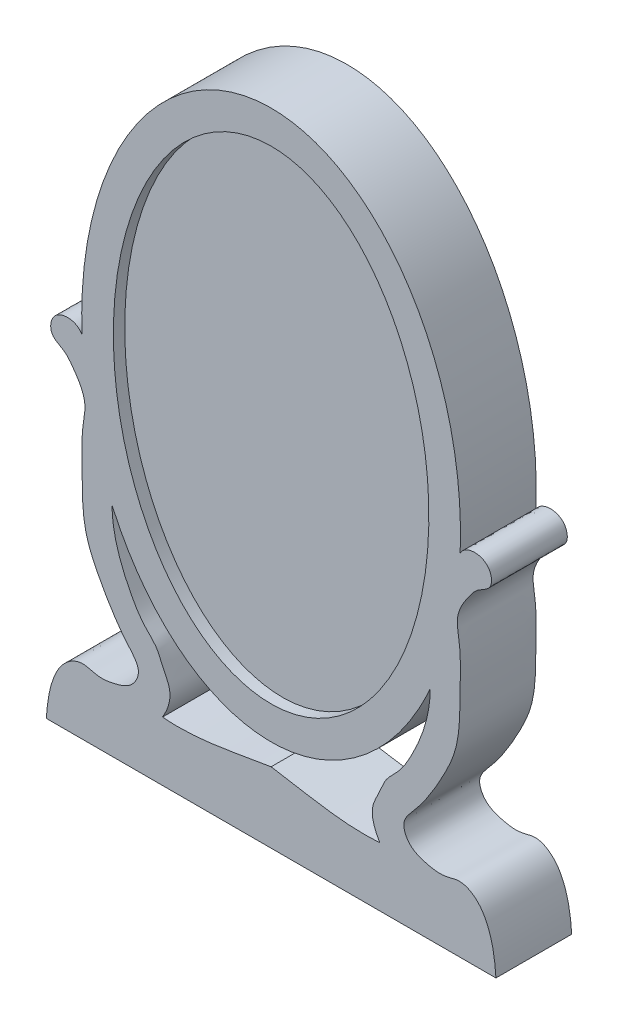
SolidWorks part; units mm, degrees
material "6061 Alloy"
ref_plane "Front Plane" through (0, 0, 0) normal (0, 0, 1) x (1, 0, 0)
ref_plane "Top Plane" through (0, 0, 0) normal (0, 1, 0) x (1, 0, 0)
ref_plane "Right Plane" through (0, 0, 0) normal (1, 0, 0) x (0, 0, -1)
sketch "Sketch1" plane through (0, 0, 0) normal (0, 0, 1) x (1, 0, 0)
  ellipse E0 centre (0, 0) end of major axis (0, 18.4068) minor radius 12.7
  ellipse E1 centre (0, 0) end of major axis (0, 16.1956) minor radius 10.5779
  dimension "D1" = 25.4
extrude "Boss-Extrude1" add sketch "Sketch1" along normal blind 5.08 contours E0 E1
sketch "Sketch3" plane through (0, 0, 0) normal (0, 0, 1) x (1, 0, 0)
  line L0 (-58.3604, 222.4715) -> (456.3062, 222.4715) construction
  line L1 (-15.0737, -24.5751) -> (15.0737, -24.5751)
  line L2 (0, -24.5751) -> (0, -16.9802) construction
  ellipse E0 centre (0, 0) end of major axis (0, 16.1956) minor radius 10.5779 construction
  ellipse E1 centre (0, 0) end of major axis (0, 16.1956) minor radius 10.5779
  ellipse E2 centre (0, 0) end of major axis (0, 18.4068) minor radius 12.7 construction
  ellipse E3 centre (0, 0) end of major axis (0, 18.4068) minor radius 12.7
  spline S0 degree 3 poles (-12.6771, -1.1047) (-13.0147, -0.4447) (-14.6864, -0.3765) (-14.9011, -2.2035) (-13.8469, -2.5536) (-13.1067, -3.5285) (-12.3218, -4.7223) (-12.5933, -6.0613) (-12.723, -7.3548) (-12.6355, -9.5358) (-12.7153, -12.1338) (-11.5521, -14.6416) (-10.5924, -16.2889) (-9.608, -17.5998) (-8.6693, -18.5874) (-9.2548, -19.8824) (-10.4033, -20.2836) (-11.5867, -20.4812) (-12.6745, -20.0175) (-13.9505, -20.6484) (-14.8367, -22.2902) (-15.0182, -23.7173) (-15.0737, -24.5751) knots 0 0 0 0 0.066937 0.100724 0.132255 0.158396 0.217811 0.257919 0.283383 0.341892 0.465467 0.523432 0.602214 0.644588 0.683893 0.717443 0.758397 0.79519 0.829587 0.863768 0.918492 1 1 1 1
  spline S1 degree 3 poles (0, -19.8465) (-2.4132, -20.2161) (-4.8225, -20.8172) (-7.2824, -20.6027) knots 0 0 0 0 1 1 1 1
  spline S2 degree 3 poles (-7.2824, -20.6027) (-6.9834, -20.1098) (-6.5175, -18.9769) (-7.2607, -17.7808) (-7.6401, -16.6788) (-8.6625, -15.8172) (-9.9534, -13.6012) (-10.6596, -11.5758) (-10.6691, -9.9847) knots 0 0 0 0 0.156869 0.26988 0.345337 0.453457 0.602335 1 1 1 1
  spline S3 degree 3 poles (12.6771, -1.1047) (13.0147, -0.4447) (14.6864, -0.3765) (14.9011, -2.2035) (13.8469, -2.5536) (13.1067, -3.5285) (12.3218, -4.7223) (12.5933, -6.0613) (12.723, -7.3548) (12.6355, -9.5358) (12.7153, -12.1338) (11.5521, -14.6416) (10.5924, -16.2889) (9.608, -17.5998) (8.6693, -18.5874) (9.2548, -19.8824) (10.4033, -20.2836) (11.5867, -20.4812) (12.6745, -20.0175) (13.9505, -20.6484) (14.8367, -22.2902) (15.0182, -23.7173) (15.0737, -24.5751) knots 0 0 0 0 0.066937 0.100724 0.132255 0.158396 0.217811 0.257919 0.283383 0.341892 0.465467 0.523432 0.602214 0.644588 0.683893 0.717443 0.758397 0.79519 0.829587 0.863768 0.918492 1 1 1 1
  spline S4 degree 3 poles (0, -19.8465) (2.4132, -20.2161) (4.8225, -20.8172) (7.2824, -20.6027) knots 0 0 0 0 1 1 1 1
  spline S5 degree 3 poles (7.2824, -20.6027) (6.9834, -20.1098) (6.5175, -18.9769) (7.2607, -17.7808) (7.6401, -16.6788) (8.6625, -15.8172) (9.9534, -13.6012) (10.6596, -11.5758) (10.6691, -9.9847) knots 0 0 0 0 0.156869 0.26988 0.345337 0.453457 0.602335 1 1 1 1
extrude "Boss-Extrude2" add sketch "Sketch3" along normal blind 5.08 contours E1 | S5 S4 S1 S2 E3 S0 L1 S3
sketch "Sketch6" plane through (0, 0, 5.08) normal (0, 0, 1) x (1, 0, 0)
  ellipse E0 centre (0, 0) end of major axis (0, 16.1956) minor radius 10.5779 construction
  ellipse E1 centre (0, 0) end of major axis (0, 16.1956) minor radius 10.5779
extrude "Cut-Extrude1" cut sketch "Sketch6" against normal blind 0.762
sketch "Sketch7" plane through (0, -24.5751, 0) normal (0, -1, 0) x (1, 0, 0)
  line L0 (-15.0737, 2.54) -> (15.0737, 2.54) construction
  line L1 (-15.0737, 5.08) -> (-15.0737, 0) construction
  line L2 (15.0737, 5.08) -> (15.0737, 0) construction
  point P8 (0, 2.54)
hole_wizard "#8-32 Tapped Hole1" positions "Sketch7" profile "Sketch8" tap size "#8-32" standard "ANSI Inch"
sketch "Sketch8" plane through (0, -24.5751, 2.54) normal (1, 0, 0) x (0, 0, -1)
  line L0 (0, 0) -> (0, 3.5778)
  line L1 (0, 3.5778) -> (1.7272, 2.54)
  line L2 (1.7272, 2.54) -> (1.7272, 0)
  line L5 (1.7272, 0) -> (0, 0)
  line L10 (0, 3.5778) -> (-1.7272, 2.54) construction
  line L11 (0, -6.35) -> (0, 107.95) construction
  dimension "Tap Drill Dia." = 3.4544
  dimension "Tap Drill Depth" = 2.54
  dimension "Drill Angle" = 118
cosmetic thread "Hole Thread1" parameters "D1"=5.08, "D2"=4.1656
